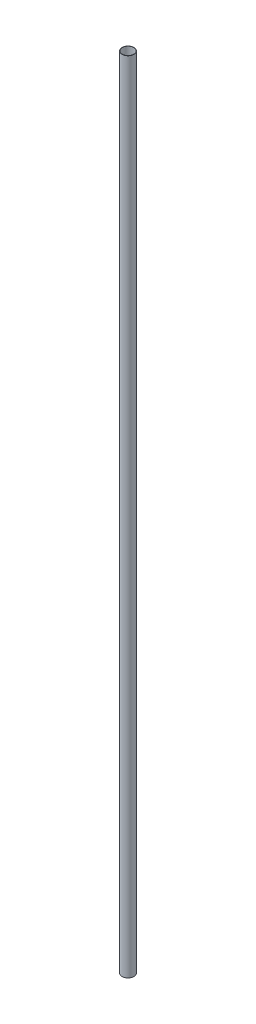
SolidWorks part; units mm, degrees
ref_plane "Front Plane" through (0, 0, 0) normal (0, 0, 1) x (1, 0, 0)
ref_plane "Top Plane" through (0, 0, 0) normal (0, 1, 0) x (1, 0, 0)
ref_plane "Right Plane" through (0, 0, 0) normal (1, 0, 0) x (0, 0, -1)
sketch "Sketch1" plane through (0, 0, 0) normal (0, 1, 0) x (1, 0, 0)
  circle A0 centre (0, 0) radius 15
  circle A1 centre (0, 0) radius 14.435
extrude "Boss-Extrude2" add sketch "Sketch1" along normal blind 2000
